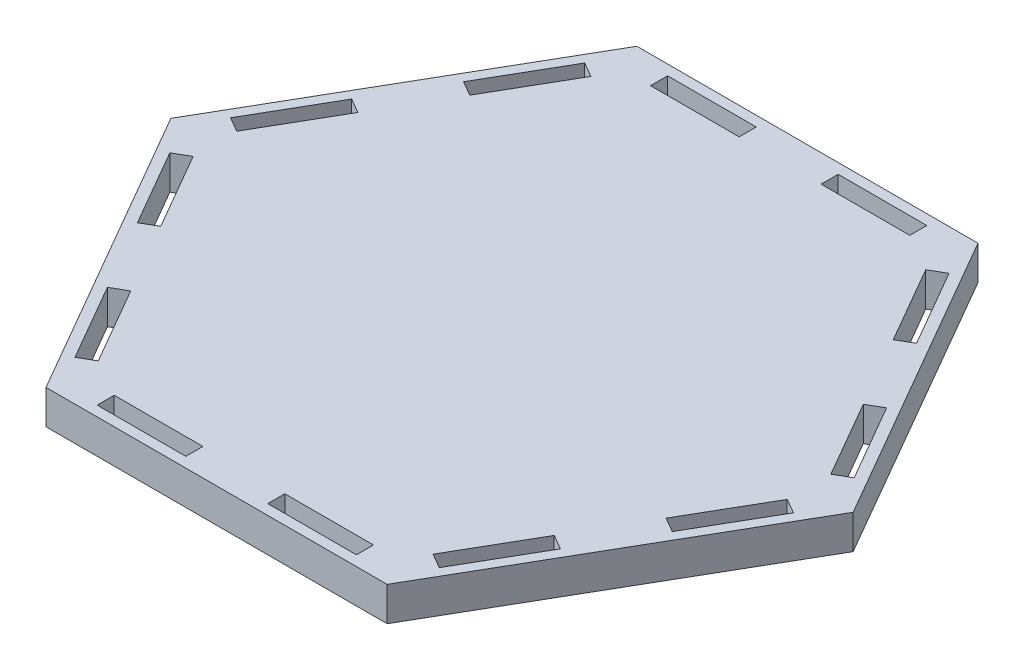
SolidWorks part; units mm, degrees
material "Cedar"
ref_plane "Front Plane" through (0, 0, 0) normal (0, 0, 1) x (1, 0, 0)
ref_plane "Top Plane" through (0, 0, 0) normal (0, 1, 0) x (1, 0, 0)
ref_plane "Right Plane" through (0, 0, 0) normal (1, 0, 0) x (0, 0, -1)
sketch "Sketch1" plane through (0, 0, 0) normal (0, 1, 0) x (1, 0, 0)
  line L0 (-63.5, 0) -> (-31.75, -54.9926)
  line L1 (63.5, 0) -> (31.75, 54.9926)
  line L2 (31.75, 54.9926) -> (-31.75, 54.9926)
  line L3 (-31.75, 54.9926) -> (-63.5, 0)
  line L4 (-31.75, -54.9926) -> (31.75, -54.9926)
  line L5 (31.75, -54.9926) -> (63.5, 0)
  line L6 (0, 0) -> (63.5, 0) construction
  circle A0 centre (0, 0) radius 54.9926 construction
  dimension "D1" = 63.5
extrude "Boss-Extrude1" add sketch "Sketch1" along normal blind 6.35
sketch "Sketch2" plane through (0, 6.35, 0) normal (0, 1, 0) x (1, 0, 0)
  line L0 (0, 0) -> (0, 36.6617) construction
  line L1 (31.75, -18.3309) -> (0, 36.6617) construction
  line L2 (0, 36.6617) -> (-31.75, -18.3309) construction
  line L3 (-31.75, -18.3309) -> (31.75, -18.3309) construction
  line L4 (-60.5671, 5.08) -> (-25.8841, -54.9926) construction
  line L5 (-31.75, 54.9926) -> (-63.5, 0) construction
  line L6 (-31.75, -54.9926) -> (31.75, -54.9926) construction
  line L7 (-63.5, 0) -> (-31.75, -54.9926) construction
  line L8 (-47.625, -27.4963) -> (-43.2256, -24.9563) construction
  line L9 (-55.2906, -4.0591) -> (-58.0402, -5.6466)
  line L10 (-58.0402, -5.6466) -> (-49.7852, -19.9447)
  line L11 (-49.7852, -19.9447) -> (-47.0356, -18.3572)
  line L12 (-47.0356, -18.3572) -> (-55.2906, -4.0591)
  line L13 (-31.1606, -45.8535) -> (-33.9102, -47.441)
  line L14 (-39.4156, -31.5554) -> (-31.1606, -45.8535)
  line L15 (-33.9102, -47.441) -> (-42.1652, -33.1429)
  line L16 (-42.1652, -33.1429) -> (-39.4156, -31.5554)
  line L17 (-25.8841, 54.9926) -> (-60.5671, -5.08) construction
  line L18 (-31.1606, 45.8535) -> (-33.9102, 47.441)
  line L19 (-33.9102, 47.441) -> (-42.1652, 33.1429)
  line L20 (-39.4156, 31.5554) -> (-31.1606, 45.8535)
  line L21 (-42.1652, 33.1429) -> (-39.4156, 31.5554)
  line L22 (-47.625, 27.4963) -> (-43.2256, 24.9563) construction
  line L23 (-49.7852, 19.9447) -> (-47.0356, 18.3572)
  line L24 (-58.0402, 5.6466) -> (-49.7852, 19.9447)
  line L25 (-47.0356, 18.3572) -> (-55.2906, 4.0591)
  line L26 (-55.2906, 4.0591) -> (-58.0402, 5.6466)
  line L27 (34.6829, 49.9126) -> (-34.6829, 49.9126) construction
  line L28 (24.13, 49.9126) -> (24.13, 53.0876)
  line L29 (24.13, 53.0876) -> (7.62, 53.0876)
  line L30 (7.62, 49.9126) -> (24.13, 49.9126)
  line L31 (7.62, 53.0876) -> (7.62, 49.9126)
  line L32 (0, 54.9926) -> (0, 49.9126) construction
  line L33 (-7.62, 53.0876) -> (-7.62, 49.9126)
  line L34 (-24.13, 53.0876) -> (-7.62, 53.0876)
  line L35 (-7.62, 49.9126) -> (-24.13, 49.9126)
  line L36 (-24.13, 49.9126) -> (-24.13, 53.0876)
  line L37 (60.5671, -5.08) -> (25.8841, 54.9926) construction
  line L38 (55.2906, 4.0591) -> (58.0402, 5.6466)
  line L39 (58.0402, 5.6466) -> (49.7852, 19.9447)
  line L40 (47.0356, 18.3572) -> (55.2906, 4.0591)
  line L41 (49.7852, 19.9447) -> (47.0356, 18.3572)
  line L42 (47.625, 27.4963) -> (43.2256, 24.9563) construction
  line L43 (42.1652, 33.1429) -> (39.4156, 31.5554)
  line L44 (33.9102, 47.441) -> (42.1652, 33.1429)
  line L45 (39.4156, 31.5554) -> (31.1606, 45.8535)
  line L46 (31.1606, 45.8535) -> (33.9102, 47.441)
  line L47 (25.8841, -54.9926) -> (60.5671, 5.08) construction
  line L48 (31.1606, -45.8535) -> (33.9102, -47.441)
  line L49 (33.9102, -47.441) -> (42.1652, -33.1429)
  line L50 (39.4156, -31.5554) -> (31.1606, -45.8535)
  line L51 (42.1652, -33.1429) -> (39.4156, -31.5554)
  line L52 (47.625, -27.4963) -> (43.2256, -24.9563) construction
  line L53 (49.7852, -19.9447) -> (47.0356, -18.3572)
  line L54 (58.0402, -5.6466) -> (49.7852, -19.9447)
  line L55 (47.0356, -18.3572) -> (55.2906, -4.0591)
  line L56 (55.2906, -4.0591) -> (58.0402, -5.6466)
  line L57 (-34.6829, -49.9126) -> (34.6829, -49.9126) construction
  line L58 (-24.13, -49.9126) -> (-24.13, -53.0876)
  line L59 (-24.13, -53.0876) -> (-7.62, -53.0876)
  line L60 (-7.62, -49.9126) -> (-24.13, -49.9126)
  line L61 (-7.62, -53.0876) -> (-7.62, -49.9126)
  line L62 (0, -54.9926) -> (0, -49.9126) construction
  line L63 (7.62, -53.0876) -> (7.62, -49.9126)
  line L64 (24.13, -53.0876) -> (7.62, -53.0876)
  line L65 (7.62, -49.9126) -> (24.13, -49.9126)
  line L66 (24.13, -49.9126) -> (24.13, -53.0876)
  circle A0 centre (0, 0) radius 18.3309 construction
  point P1 (0, 0)
  point P13 (0, 0)
  point P92 (0, 0)
  point P94 (0, 0)
  dimension "D1" = 63.5
  dimension "D4" = 5.08
  dimension "D5" = 3.175
  dimension "D6" = 16.51
  dimension "D7" = 7.62
  dimension "D8" = 6
extrude "Cut-Extrude1" cut sketch "Sketch2" against normal through all
